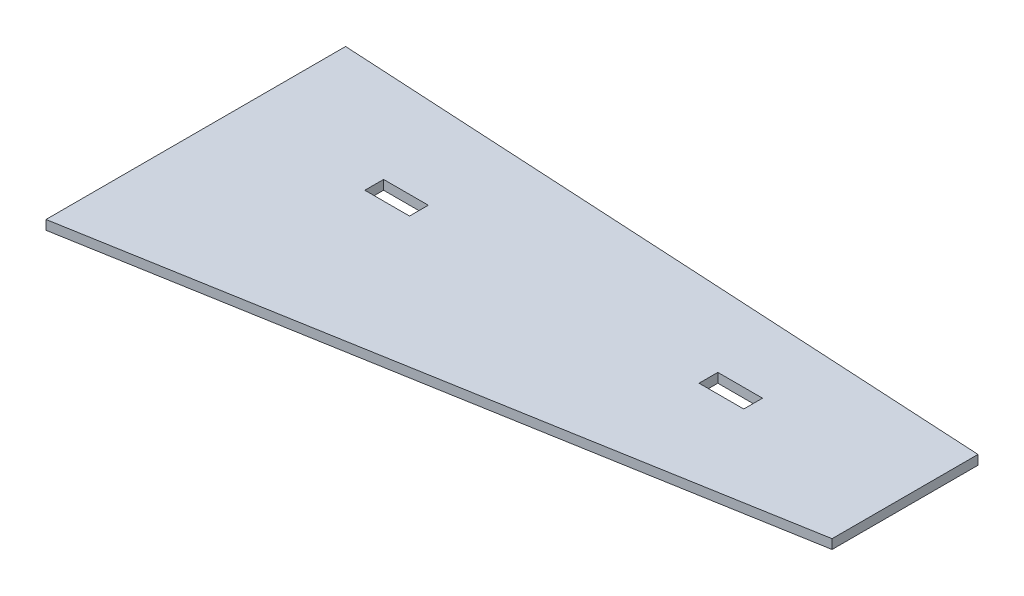
SolidWorks part; units mm, degrees
ref_plane "Front" through (0, 0, 0) normal (0, 0, 1) x (1, 0, 0)
ref_plane "Top" through (0, 0, 0) normal (0, 1, 0) x (1, 0, 0)
ref_plane "Right" through (0, 0, 0) normal (1, 0, 0) x (0, 0, -1)
sketch "Sketch1" plane through (0, 0, 0) normal (0, 1, 0) x (1, 0, 0)
  line L0 (602.1137, -343.7415) -> (602.1137, -2482.4082) construction
  line L1 (0, 0) -> (380.417, -21.0684)
  line L2 (0, 0) -> (0, -206.442) construction
  line L3 (380.417, -21.0684) -> (380.417, -103.9837)
  line L4 (380.417, -103.9837) -> (0, -170.2354)
  line L5 (0, 0) -> (0, -170.2354)
  line L6 (380.417, -21.0684) -> (455.6706, -25.2362)
  line L7 (460.8009, -126.1911) -> (0, -206.442)
  line L8 (0, -170.2354) -> (0, -206.442)
  line L9 (272.8412, -158.9253) -> (272.8412, -130.6723)
  line L10 (272.8412, -130.6723) -> (455.1314, -98.9254)
  line L11 (455.1314, -98.9254) -> (455.1314, -127.1784)
  spline S0 degree 3 poles (455.6706, -25.2362) (459.3541, -25.4402) (464.065, -27.4709) (469.9936, -39.0852) (473.4584, -72.4051) (464.1079, -102.8001) (460.8009, -126.1911) knots 0 0 0 0 0.082695 0.147079 0.342427 1 1 1 1
  dimension "D1" = 381
  dimension "D2" = 86.83
  dimension "D3" = 80.121
extrude "Base" add sketch "Sketch1" along normal blind 5.334 contours L1 L5 L4 L3
sketch "Folded Sketch" plane through (0, 5.334, 0) normal (0, 1, 0) x (1, 0, 0)
  line L0 (-24.2728, 0) -> (-24.2728, -206.5305) construction
  line L1 (0, 0) -> (380.417, -21.0684)
  line L2 (0, 0) -> (0, -206.442) construction
  line L3 (1.27, -44.45) -> (470.8001, -49.6152)
  line L4 (0.9116, -90.1699) -> (469.3093, -78.835)
  line L5 (0, 0) -> (0, -206.442)
  line L6 (380.417, -21.0684) -> (455.6706, -25.2362)
  line L7 (460.8009, -126.1911) -> (0, -206.442)
  line L8 (0, 0) -> (1.27, -44.45)
  line L9 (272.8412, -158.9253) -> (272.8412, -130.6723)
  line L10 (272.8412, -130.6723) -> (455.1314, -98.9254)
  line L11 (455.1314, -98.9254) -> (455.1314, -127.1784)
  line L12 (0, 0) -> (0, -170.2354) construction
  line L13 (1.27, -44.45) -> (0, -206.442)
  line L14 (0, 0) -> (502.0386, 0) construction
  spline S0 degree 3 poles (455.6706, -25.2362) (459.3541, -25.4402) (464.065, -27.4709) (469.9936, -39.0852) (473.4584, -72.4051) (464.1079, -102.8001) (460.8009, -126.1911) knots 0 0 0 0 0.082695 0.147079 0.342427 1 1 1 1
  dimension "D1" = 44.45
  dimension "D2" = 1.27
  dimension "D3" = 45.7213
ref_plane "Spacer Height " through (0, 18.034, 0) normal (0, 1, 0) x (1, 0, 0)
sketch "Sketch3" plane through (0, 0, 0) normal (0, -1, 0) x (1, 0, 0)
  line L8 (291.517, 54.6115) -> (291.517, 65.2795)
  line L9 (291.517, 65.2795) -> (266.117, 65.2795)
  line L10 (266.117, 65.2795) -> (266.117, 54.6115)
  line L11 (266.117, 54.6115) -> (291.517, 54.6115)
  line L12 (101.6, 54.6115) -> (101.6, 65.2795)
  line L13 (101.6, 65.2795) -> (76.2, 65.2795)
  line L14 (76.2, 65.2795) -> (76.2, 54.6115)
  line L15 (76.2, 54.6115) -> (101.6, 54.6115)
extrude "Cut-Extrude1" cut sketch "Sketch3" against normal up to next
sketch "Build Plans" plane through (0, 0, 0) normal (0, 1, 0) x (1, 0, 0)
  line L0 (-24.2728, 0) -> (-24.2728, -206.5305) construction
  line L1 (0, 0) -> (380.417, -21.0684)
  line L2 (0, 0) -> (0, -170.2354)
  line L3 (0, -170.2354) -> (380.417, -103.9837)
  line L4 (380.417, -103.9837) -> (380.417, -21.0684)
  line L5 (101.6, -54.6115) -> (101.6, -65.2795) construction
  line L6 (380.417, -21.0684) -> (455.6706, -25.2362)
  line L7 (76.2, -54.6115) -> (101.6, -54.6115) construction
  line L8 (76.2, -65.2795) -> (76.2, -54.6115) construction
  line L9 (101.6, -65.2795) -> (76.2, -65.2795) construction
  line L10 (266.117, -65.2795) -> (266.117, -54.6115) construction
  line L11 (266.117, -54.6115) -> (291.517, -54.6115) construction
  line L12 (291.517, -54.6115) -> (291.517, -65.2795) construction
  line L13 (463.2719, 48.062) -> (466.3918, 76.1422)
  line L14 (285.6022, 99.7443) -> (463.2719, 48.062)
  line L15 (288.7221, 127.8245) -> (285.6022, 99.7443)
  line L16 (471.9176, 74.5348) -> (22.7966, 205.1795)
  line L17 (10.8631, 89.5178) -> (475.1446, 26.5288)
  line L18 (6.1707, 44.0379) -> (22.7966, 205.1795)
  line L19 (0, 0) -> (6.1707, 44.0379)
  line L20 (6.1707, 44.0379) -> (473.3996, -2.6769)
  line L21 (291.517, -65.2795) -> (266.117, -65.2795) construction
  line L22 (291.517, -65.2795) -> (266.117, -65.2795)
  line L23 (291.517, -54.6115) -> (291.517, -65.2795)
  line L24 (266.117, -54.6115) -> (291.517, -54.6115)
  line L25 (266.117, -65.2795) -> (266.117, -54.6115)
  line L26 (101.6, -54.6115) -> (101.6, -65.2795)
  line L27 (101.6, -65.2795) -> (76.2, -65.2795)
  line L28 (76.2, -65.2795) -> (76.2, -54.6115)
  line L29 (76.2, -54.6115) -> (101.6, -54.6115)
  spline S1 degree 3 poles (455.6706, -25.2362) (459.3541, -25.4402) (464.2605, -23.9421) (471.4353, -13.0535) (478.5583, 19.68) (472.6214, 50.9217) (471.9176, 74.5348) knots 0 0 0 0 0.082695 0.147079 0.342427 1 1 1 1
